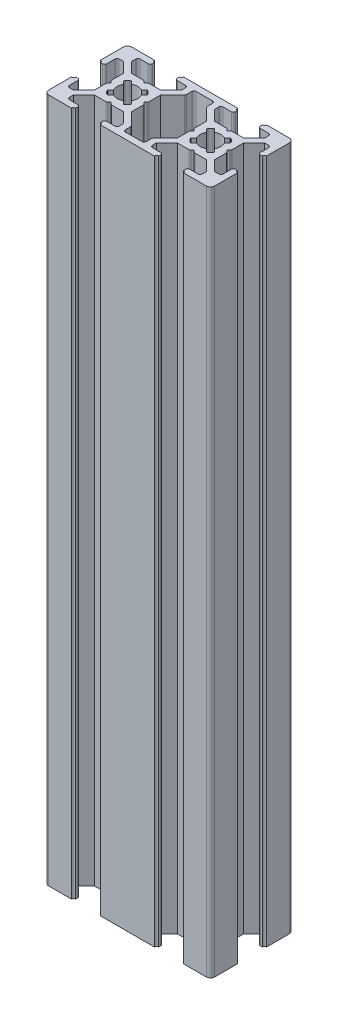
SolidWorks part; units mm, degrees
ref_plane "Front Plane" through (0, 0, 0) normal (0, 0, 1) x (1, 0, 0)
ref_plane "Top Plane" through (0, 0, 0) normal (0, 1, 0) x (1, 0, 0)
ref_plane "Right Plane" through (0, 0, 0) normal (1, 0, 0) x (0, 0, -1)
sketch "Sketch2" plane through (0, 0, 0) normal (0, 1, 0) x (1, 0, 0)
  line L0 (0, 13) -> (1.5, 13)
  line L1 (0, 0) -> (40, 0)
  line L2 (0, 0) -> (0, 20)
  line L3 (0, 20) -> (40, 20)
  line L4 (40, 0) -> (40, 20)
  line L9 (5.5, 6.5) -> (3, 4)
  line L10 (3, 4) -> (1.5, 4)
  line L11 (1.5, 4) -> (1.5, 7)
  line L12 (1.5, 7) -> (0, 7)
  line L13 (0, 7) -> (0, 13)
  line L14 (1.5, 13) -> (1.5, 16)
  line L15 (1.5, 16) -> (3, 16)
  line L16 (3, 16) -> (5.5, 13.5)
  line L17 (5.5, 10.5) -> (6, 10)
  line L18 (6, 10) -> (5.5, 9.5)
  line L19 (5.5, 9.5) -> (5.5, 10.5)
  line L20 (20, 20) -> (20, 0) construction
  line L31 (7, 18.5) -> (7, 20)
  line L32 (7, 18.5) -> (4, 18.5)
  line L33 (4, 18.5) -> (4, 17)
  line L34 (4, 17) -> (6.5, 14.5)
  line L38 (16, 18.5) -> (13, 18.5)
  line L39 (13, 18.5) -> (13, 20)
  line L40 (7, 20) -> (13, 20)
  line L41 (16, 18.5) -> (16, 17)
  line L42 (16, 17) -> (13.5, 14.5)
  line L53 (0, 10) -> (40, 10) construction
  line L89 (17.5, 18.5) -> (22.5, 18.5)
  line L90 (22.5, 18.5) -> (22.5, 16.5)
  line L91 (22.5, 16.5) -> (25.5, 13.5)
  line L92 (25.5, 13.5) -> (25.5, 6.5)
  line L93 (25.5, 6.5) -> (22.5, 3.5)
  line L94 (22.5, 3.5) -> (22.5, 1.5)
  line L95 (22.5, 1.5) -> (17.5, 1.5)
  line L96 (17.5, 1.5) -> (17.5, 3.5)
  line L97 (17.5, 3.5) -> (14.5, 6.5)
  line L98 (14.5, 6.5) -> (14.5, 13.5)
  line L99 (14.5, 13.5) -> (17.5, 16.5)
  line L100 (17.5, 16.5) -> (17.5, 18.5)
  line L102 (5.5, 13.5) -> (5.5, 10)
  line L103 (5.5, 10) -> (5.5, 6.5)
  line L104 (13.5, 14.5) -> (10, 14.5)
  line L105 (10, 14.5) -> (6.5, 14.5)
  line L106 (14.5, 10.5) -> (14.5, 9.5)
  line L107 (14.5, 9.5) -> (14, 10)
  line L108 (14, 10) -> (14.5, 10.5)
  line L109 (7, 18.5) -> (13, 18.5) construction
  line L110 (9.5, 14.5) -> (10.5, 14.5)
  line L111 (10.5, 14.5) -> (10, 14)
  line L112 (10, 14) -> (9.5, 14.5)
  line L113 (10.5, 5.5) -> (10, 6)
  line L114 (9.5, 5.5) -> (10.5, 5.5)
  line L115 (10, 6) -> (9.5, 5.5)
  line L116 (13.5, 5.5) -> (10, 5.5)
  line L117 (16, 3) -> (13.5, 5.5)
  line L118 (16, 1.5) -> (16, 3)
  line L119 (16, 1.5) -> (13, 1.5)
  line L120 (13, 1.5) -> (13, 0)
  line L121 (7, 0) -> (13, 0)
  line L122 (7, 1.5) -> (7, 0)
  line L123 (7, 1.5) -> (4, 1.5)
  line L124 (4, 1.5) -> (4, 3)
  line L125 (4, 3) -> (6.5, 5.5)
  line L126 (10, 5.5) -> (6.5, 5.5)
  line L127 (30.5, 5.5) -> (29.5, 5.5)
  line L128 (30, 6) -> (30.5, 5.5)
  line L129 (29.5, 5.5) -> (30, 6)
  line L130 (24, 3) -> (26.5, 5.5)
  line L131 (24, 1.5) -> (24, 3)
  line L132 (24, 1.5) -> (27, 1.5)
  line L133 (27, 1.5) -> (27, 0)
  line L134 (33, 0) -> (27, 0)
  line L135 (33, 1.5) -> (33, 0)
  line L136 (33, 1.5) -> (36, 1.5)
  line L137 (36, 1.5) -> (36, 3)
  line L138 (36, 3) -> (33.5, 5.5)
  line L139 (30, 5.5) -> (33.5, 5.5)
  line L140 (26.5, 5.5) -> (30, 5.5)
  line L141 (34, 10) -> (34.5, 9.5)
  line L142 (34.5, 10.5) -> (34, 10)
  line L143 (34.5, 9.5) -> (34.5, 10.5)
  line L144 (34.5, 13.5) -> (34.5, 10)
  line L145 (37, 16) -> (34.5, 13.5)
  line L146 (38.5, 16) -> (37, 16)
  line L147 (38.5, 13) -> (38.5, 16)
  line L148 (40, 13) -> (38.5, 13)
  line L149 (40, 7) -> (40, 13)
  line L150 (38.5, 7) -> (40, 7)
  line L151 (38.5, 4) -> (38.5, 7)
  line L152 (37, 4) -> (38.5, 4)
  line L153 (34.5, 6.5) -> (37, 4)
  line L154 (34.5, 10) -> (34.5, 6.5)
  line L155 (29.5, 14.5) -> (30, 14)
  line L156 (30.5, 14.5) -> (29.5, 14.5)
  line L157 (30, 14) -> (30.5, 14.5)
  line L158 (26.5, 14.5) -> (30, 14.5)
  line L159 (24, 17) -> (26.5, 14.5)
  line L160 (24, 18.5) -> (24, 17)
  line L161 (24, 18.5) -> (27, 18.5)
  line L162 (27, 18.5) -> (27, 20)
  line L163 (33, 20) -> (27, 20)
  line L164 (33, 18.5) -> (33, 20)
  line L165 (33, 18.5) -> (36, 18.5)
  line L166 (36, 18.5) -> (36, 17)
  line L167 (36, 17) -> (33.5, 14.5)
  line L168 (30, 14.5) -> (33.5, 14.5)
  line L169 (13.5, 14.5) -> (14.5, 13.5) construction
  line L170 (5.5, 6.5) -> (6.5, 5.5) construction
  line L171 (6.5, 14.5) -> (5.5, 13.5) construction
  line L172 (14.5, 6.5) -> (13.5, 5.5) construction
  line L173 (14.5, 10.5) -> (10.5, 14.5) construction
  line L174 (10.5, 5.5) -> (14.5, 9.5) construction
  line L175 (9.5, 5.5) -> (5.5, 9.5) construction
  line L176 (5.5, 10.5) -> (9.5, 14.5) construction
  line L177 (12, 13) -> (13, 12)
  line L178 (13, 12) -> (8, 7)
  line L179 (8, 7) -> (7, 8)
  line L180 (7, 8) -> (12, 13)
  line L181 (8, 13) -> (13, 8)
  line L182 (13, 8) -> (12, 7)
  line L183 (12, 7) -> (7, 12)
  line L184 (7, 12) -> (8, 13)
  line L185 (28, 7) -> (33, 12)
  line L186 (27, 8) -> (28, 7)
  line L187 (32, 13) -> (27, 8)
  line L188 (33, 12) -> (32, 13)
  line L189 (32, 7) -> (33, 8)
  line L190 (27, 12) -> (32, 7)
  line L191 (28, 13) -> (27, 12)
  line L192 (33, 8) -> (28, 13)
  line L193 (13.5, 20) -> (13, 20)
  line L194 (13, 19.5) -> (13, 20)
  line L195 (6.5, 20) -> (7, 20)
  line L196 (0, 13.5) -> (0, 13)
  line L197 (0.25, 7) -> (0, 7)
  line L198 (7, 19.5) -> (7, 20)
  line L199 (0.25, 7) -> (0, 7)
  line L200 (33, 19.5) -> (33, 20)
  line L201 (33.5, 20) -> (33, 20)
  line L202 (27, 19.5) -> (27, 20)
  line L203 (26.5, 20) -> (27, 20)
  line L204 (33, 0.5) -> (33, 0)
  line L205 (33.5, 0) -> (33, 0)
  line L206 (27, 0.5) -> (27, 0)
  line L207 (26.5, 0) -> (27, 0)
  line L208 (13, 0.5) -> (13, 0)
  line L209 (13.5, 0) -> (13, 0)
  line L210 (7, 0.5) -> (7, 0)
  line L211 (6.5, 0) -> (7, 0)
  line L212 (0.5, 13) -> (0, 13)
  line L213 (0, 6.75) -> (0, 7)
  line L214 (0, 6.75) -> (0, 7)
  line L215 (0, 7) -> (0.25, 7)
  line L216 (0, 6.5) -> (0, 7)
  line L217 (0, 7) -> (0.5, 7)
  line L218 (39.5, 13) -> (40, 13)
  line L219 (40, 13.5) -> (40, 13)
  line L220 (40, 6.5) -> (40, 7)
  line L221 (40, 7) -> (39.5, 7)
  line L222 (25.5, 9.5) -> (26, 10)
  line L223 (25.5, 10.5) -> (25.5, 9.5)
  line L224 (26, 10) -> (25.5, 10.5)
  circle A0 centre (10, 10) radius 2.5
  circle A1 centre (30, 10) radius 2.5
  arc A2 (13.5, 20) -> (13, 19.5) centre (13, 20) cw
  arc A3 (7, 19.5) -> (6.5, 20) centre (7, 20) cw
  arc A4 (0.5, 13) -> (0, 13.5) centre (0, 13) ccw
  arc A5 (0.5, 7) -> (0, 6.5) centre (0, 7) cw
  arc A6 (33, 19.5) -> (33.5, 20) centre (33, 20) ccw
  arc A7 (26.5, 20) -> (27, 19.5) centre (27, 20) ccw
  arc A8 (33, 0.5) -> (33.5, 0) centre (33, 0) cw
  arc A9 (26.5, 0) -> (27, 0.5) centre (27, 0) cw
  arc A10 (13.5, 0) -> (13, 0.5) centre (13, 0) ccw
  arc A11 (7, 0.5) -> (6.5, 0) centre (7, 0) ccw
  arc A12 (39.5, 13) -> (40, 13.5) centre (40, 13) cw
  arc A13 (39.5, 7) -> (40, 6.5) centre (40, 7) ccw
  point P19 (20, 10)
  point P103 (14.5, 10)
  dimension "D31" = 5
  dimension "D32" = 0.5
  dimension "D33" = 0.5
  dimension "D34" = 0.5
  dimension "D35" = 0.5
  dimension "D1" = 40
  dimension "D2" = 20
  dimension "D3" = 7
  dimension "D4" = 7
  dimension "D5" = 1.5
  dimension "D6" = 1.5
  dimension "D7" = 3.5
  dimension "D8" = 1.5
  dimension "D9" = 1.5
  dimension "D10" = 3
  dimension "D11" = 3
  dimension "D12" = 3.5
  dimension "D13" = 0.5
  dimension "D14" = 0.5
  dimension "D15" = 7
  dimension "D16" = 6
  dimension "D17" = 1.5
  dimension "D18" = 1.5
  dimension "D19" = 3
  dimension "D20" = 3
  dimension "D21" = 0.5
  dimension "D22" = 1.5
  dimension "D23" = 5.5
  dimension "D24" = 0.5
  dimension "D25" = 0.5
  dimension "D26" = 1.5
  dimension "D27" = 1.5
  dimension "D28" = 2
  dimension "D29" = 2
  dimension "D30" = 0.5
extrude "Boss-Extrude1" add sketch "Sketch2" along normal blind 165 contours L168 L157 L155 L158 L159 L160 L161 L162 L3 L39 L38 L41 L42 L104 L111 L112 L105 L34 L33 L32 L31 L2 L0 L14 L15 L16 L102 L17 L18 L103 L9 L10 L11 L12 L1 L122 L123 L124 L125 L126 L115 L113 L116 L117 L118 L119 L120 L133
fillet "Fillet1" radius 1 4 edges at (40, 82.5, -20) (40, 82.5, 0) (0, 82.5, 0) (0, 82.5, -20)
fillet "Fillet2" radius 0.5 6 edges at (13, 82.5, -18.5) (16, 82.5, -18.5) (10.5, 82.5, -14.5) (9.5, 82.5, -14.5) (4, 82.5, -18.5) (7, 82.5, -18.5)
fillet "Fillet3" radius 0.25 8 edges at (8, 82.5, -7) (7, 82.5, -8) (12, 82.5, -7) (13, 82.5, -8) (13, 82.5, -12) (12, 82.5, -13) (7, 82.5, -12) (8, 82.5, -13)
fillet "Fillet5" radius 0.25 8 edges at (27, 82.5, -8) (28, 82.5, -7) (32, 82.5, -7) (33, 82.5, -8) (33, 82.5, -12) (32, 82.5, -13) (27, 82.5, -12) (28, 82.5, -13)
fillet "Fillet6" radius 0.5 30 edges at (36, 82.5, -18.5) (33, 82.5, -18.5) (30.5, 82.5, -14.5) (29.5, 82.5, -14.5) (24, 82.5, -18.5) (27, 82.5, -18.5) (38.5, 82.5, -4) (38.5, 82.5, -7) (34.5, 82.5, -9.5) (34.5, 82.5, -10.5) (38.5, 82.5, -16) (38.5, 82.5, -13) (24, 82.5, -1.5) (27, 82.5, -1.5) (29.5, 82.5, -5.5) (30.5, 82.5, -5.5) (36, 82.5, -1.5) (33, 82.5, -1.5) (4, 82.5, -1.5) (7, 82.5, -1.5) (9.5, 82.5, -5.5) (10.5, 82.5, -5.5) (16, 82.5, -1.5) (13, 82.5, -1.5) (5.5, 82.5, -10.5) (5.5, 82.5, -9.5) (1.5, 82.5, -4) (1.5, 82.5, -7) (1.5, 82.5, -16) (1.5, 82.5, -13)
fillet "Fillet7" radius 0.5 8 edges at (22.5, 82.5, -3.5) (22.5, 82.5, -1.5) (17.5, 82.5, -3.5) (17.5, 82.5, -1.5) (17.5, 82.5, -16.5) (22.5, 82.5, -16.5) (22.5, 82.5, -18.5) (17.5, 82.5, -18.5)
fillet "Fillet8" radius 0.5 4 edges at (25.5, 82.5, -9.5) (25.5, 82.5, -10.5) (14.5, 82.5, -9.5) (14.5, 82.5, -10.5)
